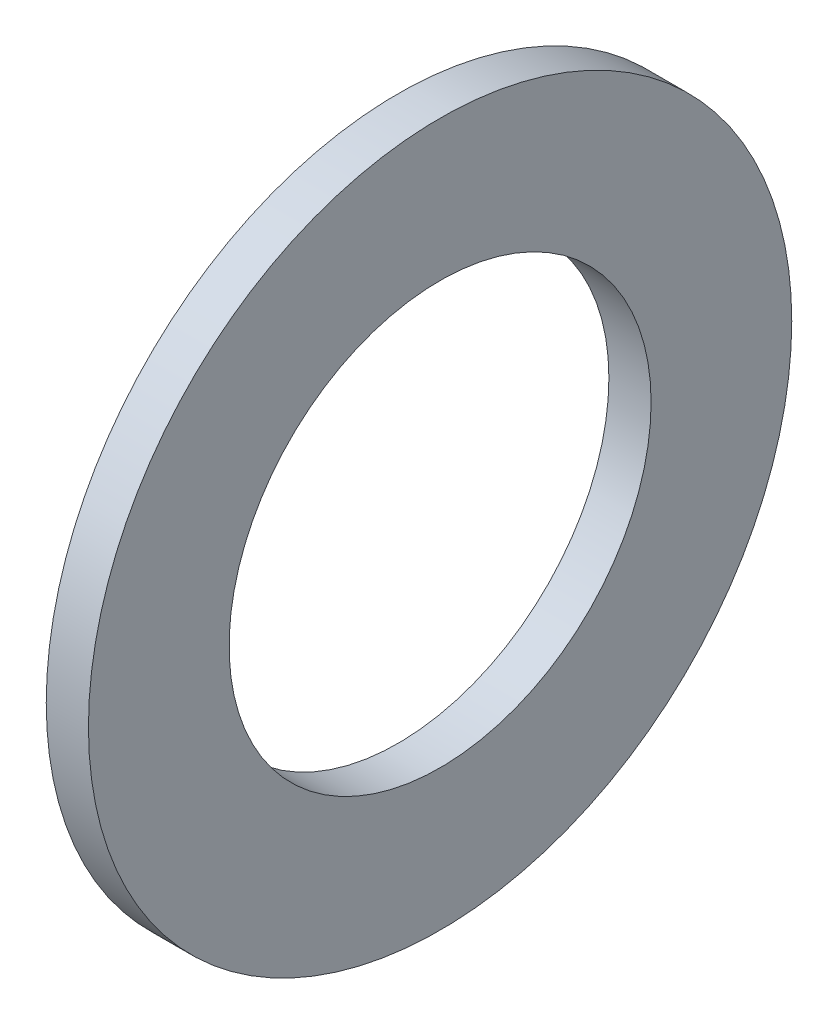
SolidWorks part; units mm, degrees
ref_plane "Front Plane" through (0, 0, 0) normal (0, 0, 1) x (1, 0, 0)
ref_plane "Top Plane" through (0, 0, 0) normal (0, 1, 0) x (1, 0, 0)
ref_plane "Right Plane" through (0, 0, 0) normal (1, 0, 0) x (0, 0, -1)
sketch "Sketch1" plane through (0, 0, 0) normal (1, 0, 0) x (0, 0, -1)
  circle A0 centre (0, 0) radius 3.81
  circle A1 centre (0, 0) radius 6.35
extrude "Boss-Extrude1" add sketch "Sketch1" along normal blind 0.762
